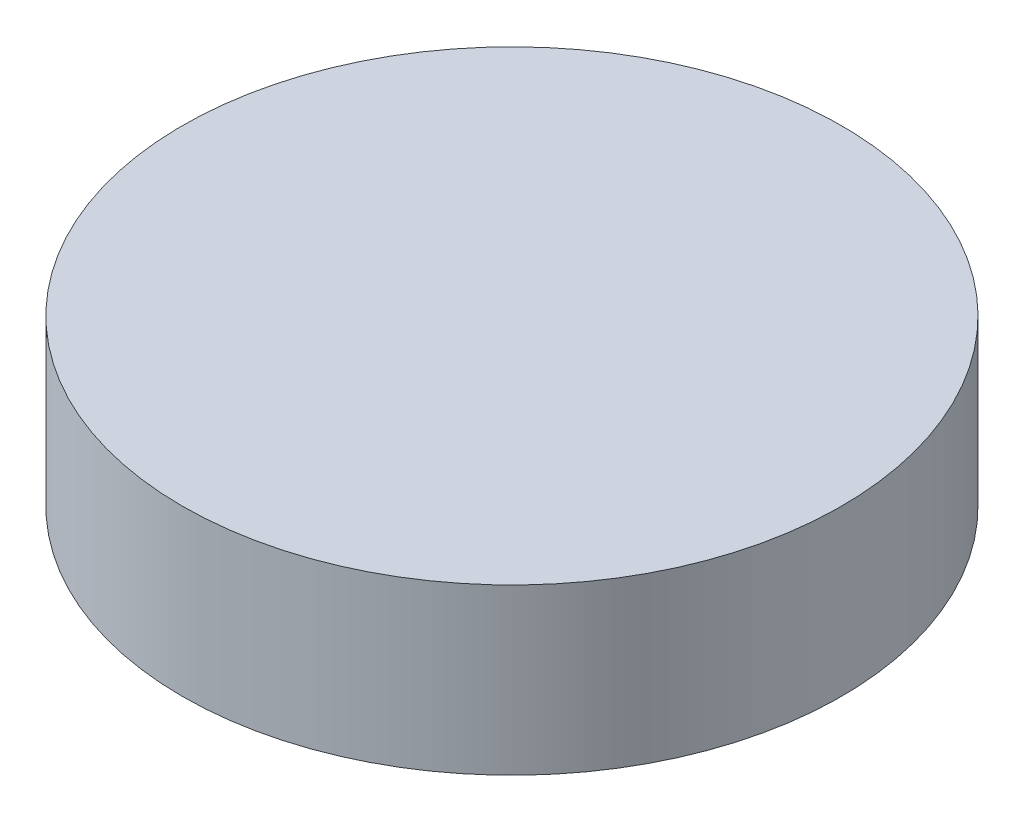
SolidWorks part; units mm, degrees
ref_plane "Front Plane" through (0, 0, 0) normal (0, 0, 1) x (1, 0, 0)
ref_plane "Top Plane" through (0, 0, 0) normal (0, 1, 0) x (1, 0, 0)
ref_plane "Right Plane" through (0, 0, 0) normal (1, 0, 0) x (0, 0, -1)
sketch "Sketch1" plane through (0, 0, 0) normal (0, 1, 0) x (1, 0, 0)
  circle A0 centre (0, 0) radius 25.4
  dimension "D1" = 50.8
extrude "Boss-Extrude1" add sketch "Sketch1" along normal mid plane 12.7
